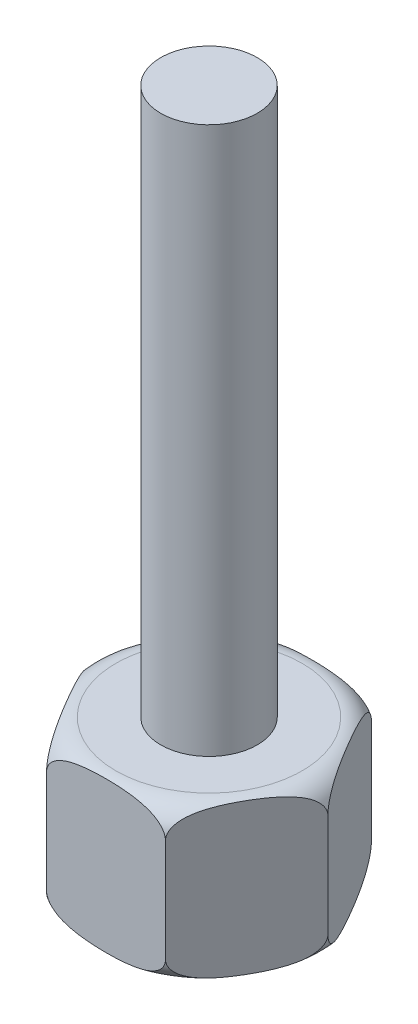
SolidWorks part; units mm, degrees
ref_plane "Front Plane" through (0, 0, 0) normal (0, 0, 1) x (1, 0, 0)
ref_plane "Top Plane" through (0, 0, 0) normal (0, 1, 0) x (1, 0, 0)
ref_plane "Right Plane" through (0, 0, 0) normal (1, 0, 0) x (0, 0, -1)
sketch "Sketch1" plane through (0, 0, 0) normal (0, 1, 0) x (1, 0, 0)
  line L1 (4.6188, 0) -> (2.3094, 4)
  line L2 (2.3094, 4) -> (-2.3094, 4)
  line L3 (-2.3094, 4) -> (-4.6188, 0)
  line L4 (-4.6188, 0) -> (-2.3094, -4)
  line L5 (-2.3094, -4) -> (2.3094, -4)
  line L6 (2.3094, -4) -> (4.6188, 0)
  circle A0 centre (0, 0) radius 4 construction
  point P1 (0, 0)
  dimension "D1" = 8
extrude "Boss-Extrude1" add sketch "Sketch1" along normal blind 6
sketch "Sketch2" plane through (0, 6, 0) normal (0, 1, 0) x (1, 0, 0)
  circle A0 centre (0, 0) radius 1.875
  dimension "D1" = 3.75
extrude "Boss-Extrude2" add sketch "Sketch2" along normal blind 21.25
sketch "Sketch3" plane through (0, 0, 0) normal (0, 0, 1) x (1, 0, 0)
  line L0 (2.3094, 0) -> (4.6188, 0) construction
  line L2 (2.3094, 6) -> (4.6188, 6) construction
  line L3 (4.6188, 0) -> (3.6188, 0)
  line L4 (4.6188, 5) -> (4.6188, 6)
  line L5 (4.6188, 6) -> (3.6188, 6)
  line L6 (4.6188, 1) -> (4.6188, 0)
  line L7 (0, 0) -> (0, -1.4429) construction
  arc A0 (4.6188, 1) -> (3.6188, 0) centre (3.6188, 1) cw
  arc A1 (4.6188, 5) -> (3.6188, 6) centre (3.6188, 5) ccw
  dimension "D1" = 1
revolve "Cut-Revolve1" cut sketch "Sketch3" angle 360 about L7
